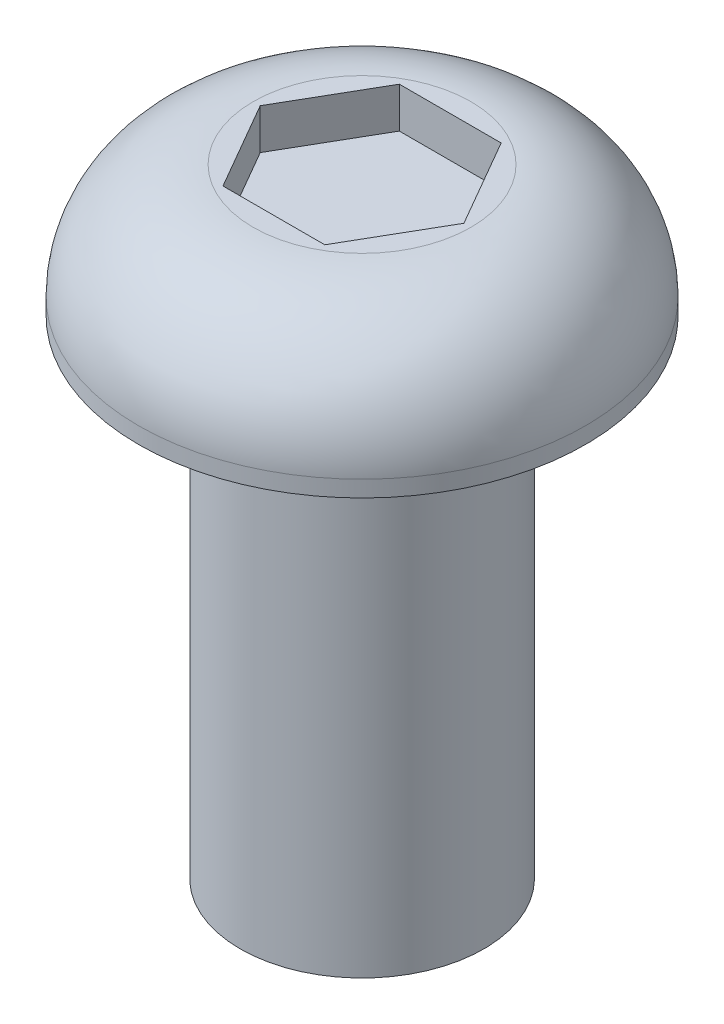
SolidWorks part; units mm, degrees
ref_plane "Front Plane" through (0, 0, 0) normal (0, 0, 1) x (1, 0, 0)
ref_plane "Top Plane" through (0, 0, 0) normal (0, 1, 0) x (1, 0, 0)
ref_plane "Right Plane" through (0, 0, 0) normal (1, 0, 0) x (0, 0, -1)
sketch "Sketch1" plane through (0, 0, 0) normal (0, 0, 1) x (1, 0, 0)
  line L0 (0, 9.0838) -> (0, 0) construction
  line L1 (0, 1.61) -> (1.34, 1.61)
  line L2 (2.75, 0.2) -> (2.75, 0)
  line L3 (2.75, 0) -> (1.5, 0)
  line L4 (1.5, 0) -> (1.5, -6)
  line L5 (1.5, -6) -> (0, -6)
  line L6 (0, 1.61) -> (0, -6)
  arc A0 (1.34, 1.61) -> (2.75, 0.2) centre (1.34, 0.2) cw
  dimension "D1" = 3
  dimension "D2" = 5.5
  dimension "D3" = 1.61
  dimension "D4" = 0.2
  dimension "D5" = 6
revolve "Revolve1" add sketch "Sketch1" angle 360 about L0
sketch "Sketch2" plane through (0, 1.61, 0) normal (0, 1, 0) x (1, 0, 0)
  line L1 (0.6265, 1.0852) -> (-0.6265, 1.0852)
  line L2 (-0.6265, 1.0852) -> (-1.2531, 0)
  line L3 (-1.2531, 0) -> (-0.6265, -1.0852)
  line L4 (-0.6265, -1.0852) -> (0.6265, -1.0852)
  line L5 (0.6265, -1.0852) -> (1.2531, 0)
  line L6 (1.2531, 0) -> (0.6265, 1.0852)
  circle A0 centre (0, 0) radius 1.0852 construction
extrude "Cut-Extrude1" cut sketch "Sketch2" against normal blind 0.5
